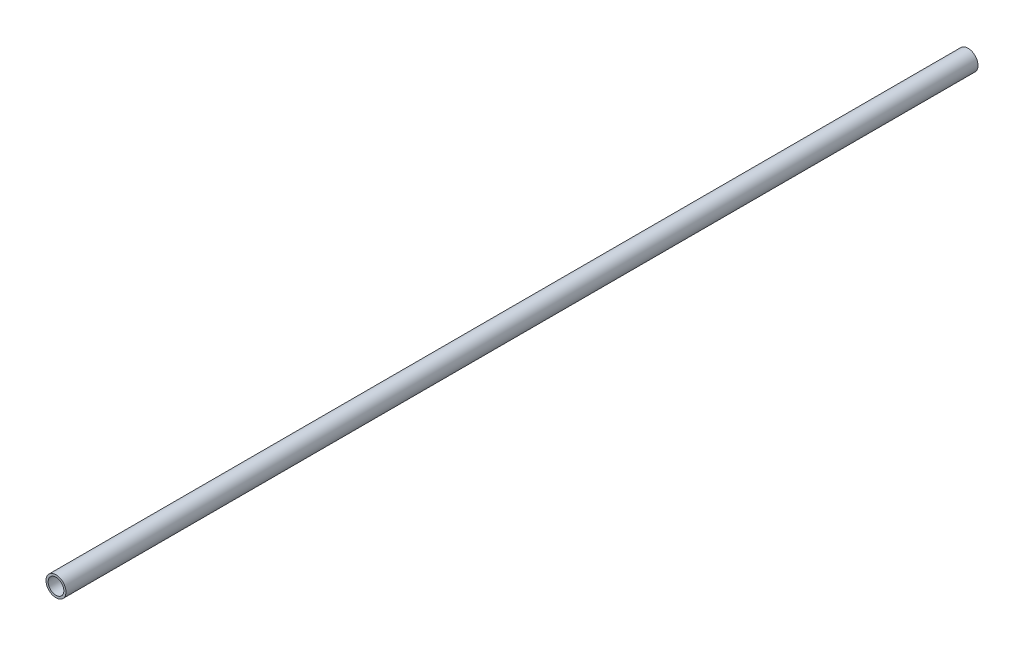
SolidWorks part; units mm, degrees
material "PVC 0.007 Plasticized"
ref_plane "Front Plane" through (0, 0, 0) normal (0, 0, 1) x (1, 0, 0)
ref_plane "Top Plane" through (0, 0, 0) normal (0, 1, 0) x (1, 0, 0)
ref_plane "Right Plane" through (0, 0, 0) normal (1, 0, 0) x (0, 0, -1)
sketch "Sketch1" plane through (0, 0, 0) normal (0, 0, 1) x (1, 0, 0)
  line L0 (10.4648, 0) -> (13.335, 0) construction
  circle A0 centre (0, 0) radius 13.335 construction
  circle A1 centre (0, 0) radius 10.4648 construction
  dimension "ID" = 20.9296
  dimension "OD" = 26.67
  dimension "Wall Thickness" = 2.8702
sketch "Sketch2" plane through (0, 0, 0) normal (1, 0, 0) x (0, 0, -1)
  line L0 (-762, 0) -> (762, 0) construction
  line L1 (-728.6625, 13.335) -> (-728.6625, -13.335) construction
  line L2 (728.6625, 13.335) -> (728.6625, -13.335) construction
  point P4 (0, 0)
  point P8 (-728.6625, 0)
  point P11 (728.6625, 0)
  dimension "Length" = 1524
  dimension "D1" = 33.3375
  dimension "D2" = 33.3375
  dimension "D3" = 26.67
sketch "Sketch3" plane through (0, 0, 0) normal (0, 0, 1) x (1, 0, 0)
  circle A0 centre (0, 0) radius 13.335
  circle A1 centre (0, 0) radius 13.335 construction
  circle A2 centre (0, 0) radius 10.4648 construction
  circle A3 centre (0, 0) radius 10.4648
extrude "Boss-Extrude1" add sketch "Sketch3" along normal up to vertex (762 mm away) and the other way up to vertex (762 mm away) up to point (0, 0, 762) other way up to point (0, 0, -762)
sketch "Sketch4" plane through (0, 0, 762) normal (0, 0, 1) x (1, 0, 0)
  circle A0 centre (0, 0) radius 10.4648 construction
  circle A1 centre (0, 0) radius 13.335
  circle A2 centre (0, 0) radius 13.335
  circle A3 centre (0, 0) radius 10.4648
  dimension "D1" = 0
extrude "Cut-Extrude2" cut sketch "Sketch4" against normal offset from surface (307.3567 mm away) 1216.6433 up to face at (10.4648, 0, -762)
equation "\"D1@Sketch2\"=\"OD@Sketch1\" * 1.25"
equation "\"D2@Sketch2\"=\"D1@Sketch2\""
equation "\"D3@Sketch2\"= \"OD@Sketch1\""
